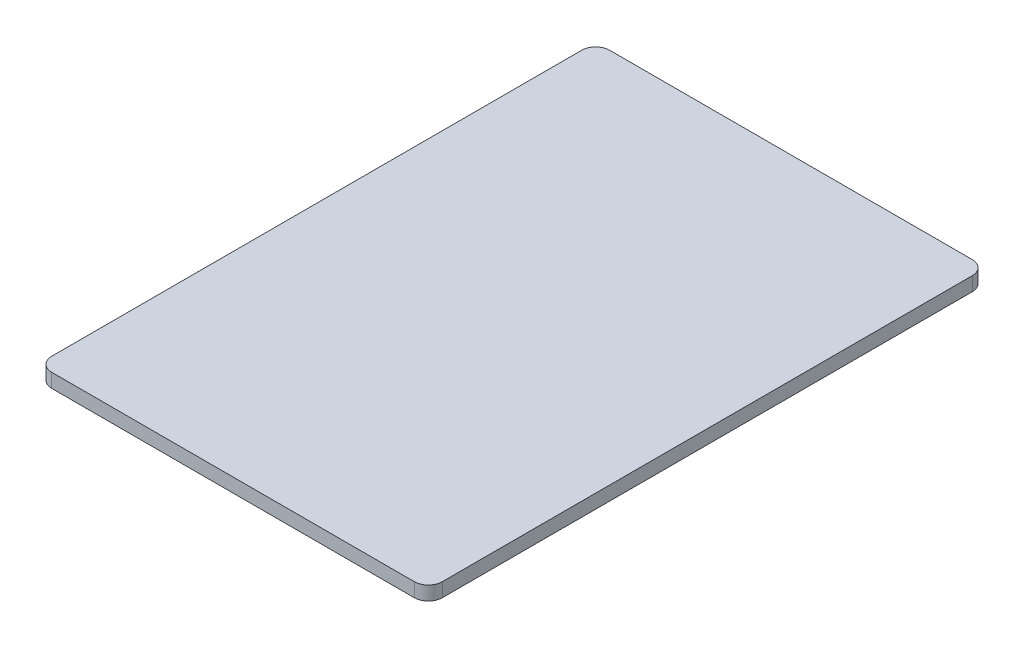
SolidWorks part; units mm, degrees
ref_plane "Front Plane" through (0, 0, 0) normal (0, 0, 1) x (1, 0, 0)
ref_plane "Top Plane" through (0, 0, 0) normal (0, 1, 0) x (1, 0, 0)
ref_plane "Right Plane" through (0, 0, 0) normal (1, 0, 0) x (0, 0, -1)
sketch "Sketch1" plane through (0, 0, 0) normal (0, 1, 0) x (1, 0, 0)
  line L0 (0, 84.3465) -> (0, -87.8658) construction
  line L1 (-97.6026, 0) -> (105.3451, 0) construction
  line L2 (-22.225, -30.1625) -> (-22.225, 30.1625)
  line L3 (-20.6375, 31.75) -> (20.6375, 31.75)
  line L4 (22.225, -30.1625) -> (22.225, 30.1625)
  line L5 (-20.6375, -31.75) -> (20.6375, -31.75)
  arc A0 (-20.6375, -31.75) -> (-22.225, -30.1625) centre (-20.6375, -30.1625) cw
  arc A1 (20.6375, -31.75) -> (22.225, -30.1625) centre (20.6375, -30.1625) ccw
  arc A2 (22.225, 30.1625) -> (20.6375, 31.75) centre (20.6375, 30.1625) ccw
  arc A3 (-22.225, 30.1625) -> (-20.6375, 31.75) centre (-20.6375, 30.1625) cw
  point P5 (0, -31.75)
  point P9 (0, 31.75)
  point P11 (22.225, 0)
  point P12 (-22.225, 0)
  point P15 (-22.225, -31.75)
  point P18 (22.225, -31.75)
  point P21 (22.225, 31.75)
  point P24 (-22.225, 31.75)
  dimension "D1" = 1.5875
  dimension "D2" = 63.5
  dimension "D3" = 44.45
extrude "Boss-Extrude1" add sketch "Sketch1" along normal blind 1.5875
